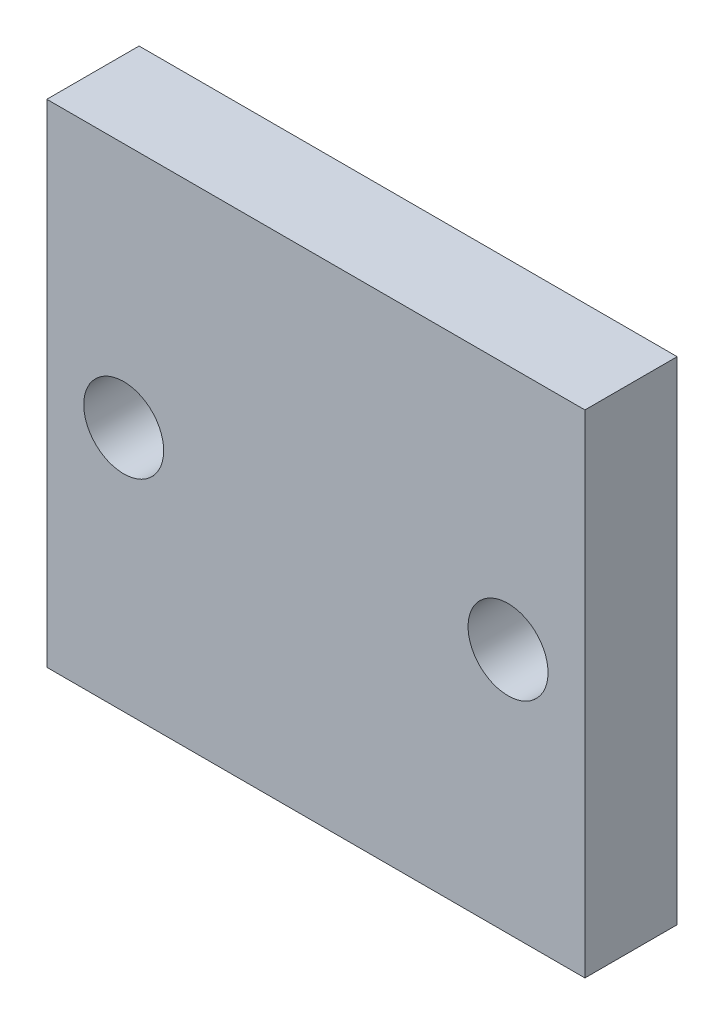
SolidWorks part; units mm, degrees
material "MDF"
ref_plane "Plano frontal" through (0, 0, 0) normal (0, 0, 1) x (1, 0, 0)
ref_plane "Plano superior" through (0, 0, 0) normal (0, 1, 0) x (1, 0, 0)
ref_plane "Plano direito" through (0, 0, 0) normal (1, 0, 0) x (0, 0, -1)
sketch "Esboço1" plane through (0, 0, 0) normal (0, 0, 1) x (1, 0, 0)
  line L0 (-12.5, 0) -> (12.5, 0) construction
  line L1 (-17.5, -16) -> (17.5, -16)
  line L2 (-17.5, -16) -> (-17.5, 16)
  line L3 (-17.5, 16) -> (17.5, 16)
  line L4 (17.5, -16) -> (17.5, 16)
  line L5 (-17.5, -16) -> (17.5, 16) construction
  line L6 (-17.5, 16) -> (17.5, -16) construction
  circle A1 centre (-12.5, 0) radius 2.6
  circle A2 centre (12.5, 0) radius 2.6
  point P0 (0, 0)
  dimension "D2" = 5.2
  dimension "D1" = 32
  dimension "D3" = 35
  dimension "D4" = 5
extrude "Ressalto-extrusão1" add sketch "Esboço1" along normal blind 6
